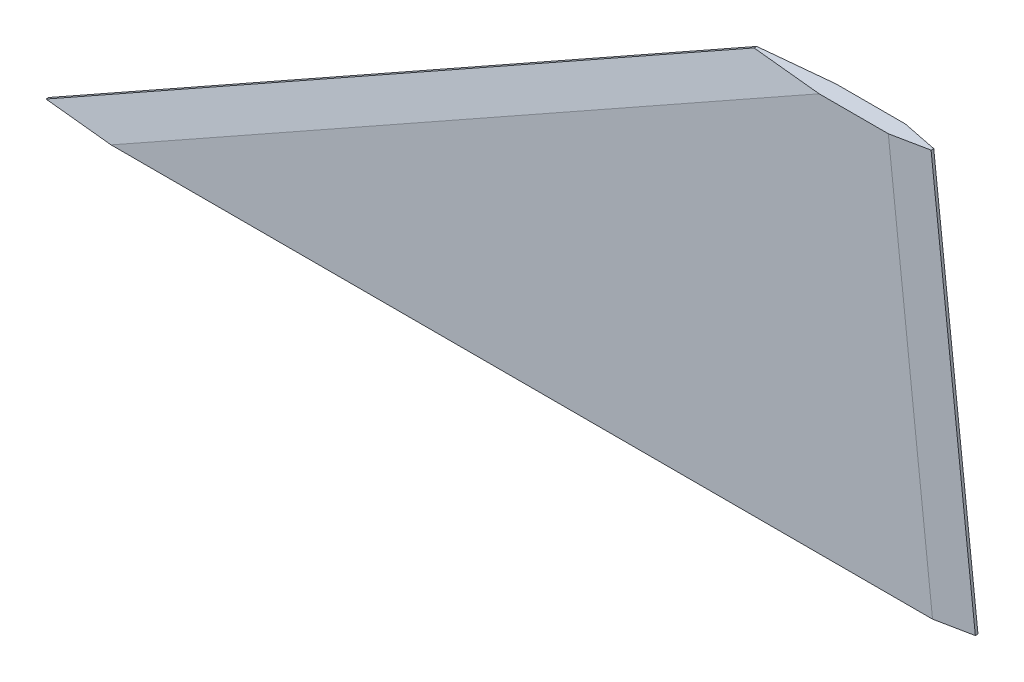
SolidWorks part; units mm, degrees
material "Wildman Fiberglass"
ref_plane "Front Plane" through (0, 0, 0) normal (0, 0, 1) x (1, 0, 0)
ref_plane "Top Plane" through (0, 0, 0) normal (0, 1, 0) x (1, 0, 0)
ref_plane "Right Plane" through (0, 0, 0) normal (1, 0, 0) x (0, 0, -1)
sketch "Sketch1" plane through (0, 0, 0) normal (0, 0, 1) x (1, 0, 0)
  line L0 (0, 0) -> (101.6, 57.15)
  line L1 (101.6, 57.15) -> (127, 57.15)
  line L2 (127, 57.15) -> (133.35, 0)
  line L3 (133.35, 0) -> (0, 0)
  line L4 (0, 0) -> (0, 57.15) construction
  line L5 (0, 57.15) -> (101.6, 57.15) construction
  dimension "D1" = 133.35
  dimension "D2" = 25.4
  dimension "D3" = 57.15
  dimension "D4" = 101.6
extrude "Boss-Extrude1" add sketch "Sketch1" along normal mid plane 2.4384
chamfer "Chamfer1" distance 5.08 distance2 1.0287 2 edges at (50.8, 28.575, 1.2192) (50.8, 28.575, -1.2192)
chamfer "Chamfer2" distance 5.08 distance2 1.0287 2 edges at (130.175, 28.575, 1.2192) (130.175, 28.575, -1.2192)
ref_plane "Plane3" through (133.35, 0, 0) normal (1, 0, 0) x (0, 0, -1)
